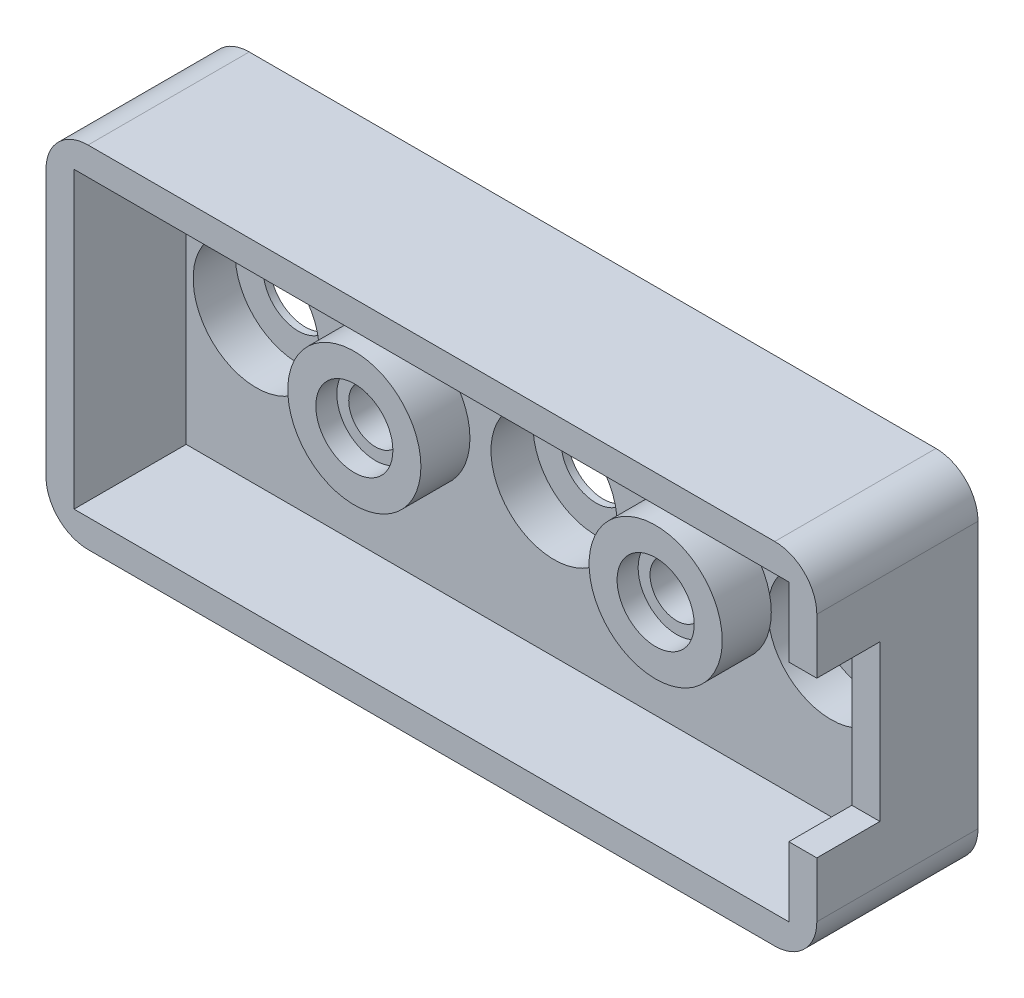
SolidWorks part; units mm, degrees
ref_plane "Alzado" through (0, 0, 0) normal (0, 0, 1) x (1, 0, 0)
ref_plane "Planta" through (0, 0, 0) normal (0, 1, 0) x (1, 0, 0)
ref_plane "Vista lateral" through (0, 0, 0) normal (1, 0, 0) x (0, 0, -1)
sketch "Croquis1" plane through (0, 0, 0) normal (0, 0, 1) x (1, 0, 0)
  line L0 (-27.5, 0) -> (27.5, 0) construction
  line L1 (-27.5, 12.5) -> (27.5, 12.5)
  line L2 (-27.5, 12.5) -> (-27.5, -12.5)
  line L3 (-27.5, -12.5) -> (27.5, -12.5)
  line L4 (27.5, 12.5) -> (27.5, -12.5)
  line L5 (-27.5, 12.5) -> (27.5, -12.5) construction
  line L6 (-27.5, -12.5) -> (27.5, 12.5) construction
  circle A0 centre (-10, 0) radius 2.75
  circle A1 centre (11.5, 0) radius 2.75
  point P0 (0, 0)
  point P12 (0, 0)
  dimension "D3" = 5.5
  dimension "D4" = 17.5
  dimension "D5" = 16
  dimension "D1" = 25
  dimension "D2" = 55
extrude "Saliente-Extruir1" add sketch "Croquis1" along normal blind 2 and the other way blind 1.5
sketch "Croquis2" plane through (0, 0, 2) normal (0, 0, 1) x (1, 0, 0)
  circle A0 centre (-10, 0) radius 4.75
  circle A1 centre (11.5, 0) radius 4.75
  circle A2 centre (11.5, 0) radius 2.75
  circle A3 centre (-10, 0) radius 2.75
  circle A4 centre (11.5, 0) radius 2.75 construction
  dimension "D1" = 5.5
  dimension "D2" = 2
extrude "Saliente-Extruir2" add sketch "Croquis2" along normal blind 3.5 contours A0 | A1 | A3 | A2
sketch "Croquis3" plane through (0, 0, 2) normal (0, 0, 1) x (1, 0, 0)
  line L1 (-25.5, 10.5) -> (25.5, 10.5)
  line L2 (-25.5, 10.5) -> (-25.5, -10.5)
  line L3 (-25.5, -10.5) -> (25.5, -10.5)
  line L4 (25.5, 10.5) -> (25.5, -10.5)
  line L5 (-25.5, 10.5) -> (25.5, -10.5) construction
  line L6 (-25.5, -10.5) -> (25.5, 10.5) construction
  line L7 (-27.5, -12.5) -> (27.5, -12.5)
  line L8 (-27.5, -12.5) -> (-27.5, 12.5)
  line L9 (-27.5, 12.5) -> (27.5, 12.5)
  line L10 (27.5, -12.5) -> (27.5, 12.5)
  line L11 (-27.5, -12.5) -> (27.5, 12.5) construction
  line L12 (-27.5, 12.5) -> (27.5, -12.5) construction
  point P0 (0, 0)
  point P6 (0, 0)
  dimension "D1" = 51
  dimension "D2" = 21
extrude "Saliente-Extruir3" add sketch "Croquis3" along normal blind 8 contours L8 L7 L10 L9 | L2 L1 L4 L3
fillet "Redondeo1" radius 3 4 edges at (-27.5, 12.5, 4.25) (27.5, 12.5, 4.25) (27.5, -12.5, 4.25) (-27.5, -12.5, 4.25)
sketch "Croquis5" plane through (0, 0, 10) normal (0, 0, 1) x (1, 0, 0)
  line L0 (0, 0) -> (27.5, 0) construction
  line L1 (27.5, -9.5) -> (27.5, 9.5) construction
  line L2 (25.5, 10.5) -> (25.5, -10.5) construction
  line L3 (25.5, 5.551) -> (27.5, 5.551)
  line L4 (25.5, 5.551) -> (25.5, -5.551)
  line L5 (25.5, -5.551) -> (27.5, -5.551)
  line L6 (27.5, 5.551) -> (27.5, -5.551)
  line L7 (25.5, 5.551) -> (27.5, -5.551) construction
  line L8 (25.5, -5.551) -> (27.5, 5.551) construction
  point P5 (26.5, 0)
  dimension "D1" = 11.1021
extrude "Cortar-Extruir1" cut sketch "Croquis5" against normal blind 6
sketch "Croquis8" plane through (0, 0, 2) normal (0, 0, 1) x (1, 0, 0)
  line L0 (-25.5, 10.5) -> (25.5, 10.5) construction
  line L1 (-26.2419, 0) -> (25.5, 0) construction
  line L2 (25.5, 10.5) -> (25.5, -10.5) construction
  line L3 (25.5, 5.551) -> (25.5, -5.551) construction
  line L4 (-25.5, 10.5) -> (-25.5, -10.5) construction
  circle A0 centre (0.75, 0) radius 4.5
  circle A1 centre (-20.5, 0) radius 4.5
  circle A2 centre (20.5019, 0) radius 4.5
  circle A4 centre (11.5, 0) radius 4.75 construction
  point P14 (-20.298, 0)
  point P15 (20.5019, 0)
  dimension "D1" = 9
  dimension "D2" = 10.75
  dimension "D3" = 10.5
  dimension "D4" = 9
  dimension "D5" = 9
  dimension "D6" = 4.9981
  dimension "D7" = 5
extrude "Cortar-Extruir4" cut sketch "Croquis8" against normal blind 3 contours A0 | A1 | A2
sketch "Croquis11" plane through (0, 0, -1.5) normal (0, 0, -1) x (-1, 0, 0)
  circle A0 centre (-11.5, 0) radius 2.75
  circle A1 centre (10, 0) radius 2.75
extrude "Saliente-Extruir5" add sketch "Croquis11" against normal blind 5.5
sketch "Croquis12" plane through (0, 0, 2) normal (0, 0, 1) x (1, 0, 0)
  circle A0 centre (-10, 0) radius 1.9
  circle A1 centre (11.5, 0) radius 1.9
  dimension "D1" = 3.8
extrude "Cortar-Extruir11" cut sketch "Croquis12" against normal through all and the other way through all
sketch "Croquis13" plane through (0, 0, 2) normal (0, 0, 1) x (1, 0, 0)
  circle A0 centre (20.5019, 0) radius 2.5
  circle A1 centre (0.75, 0) radius 2.5
  circle A2 centre (-20.5, 0) radius 2.5
  dimension "D1" = 5
extrude "Cortar-Extruir12" cut sketch "Croquis13" against normal through all
sketch "Croquis14" plane through (27.5, 0, 0) normal (1, 0, 0) x (0, 0, -1)
  line L0 (-4, -5.551) -> (-10, -5.551) construction
  line L1 (-4, 5.551) -> (-5.5, 5.551)
  line L2 (-4, 5.551) -> (-4, -5.551)
  line L3 (-4, -5.551) -> (-5.5, -5.551)
  line L4 (-5.5, 5.551) -> (-5.5, -5.551)
  dimension "D1" = 1.5
extrude "Saliente-Extruir6" add sketch "Croquis14" against normal blind 2
